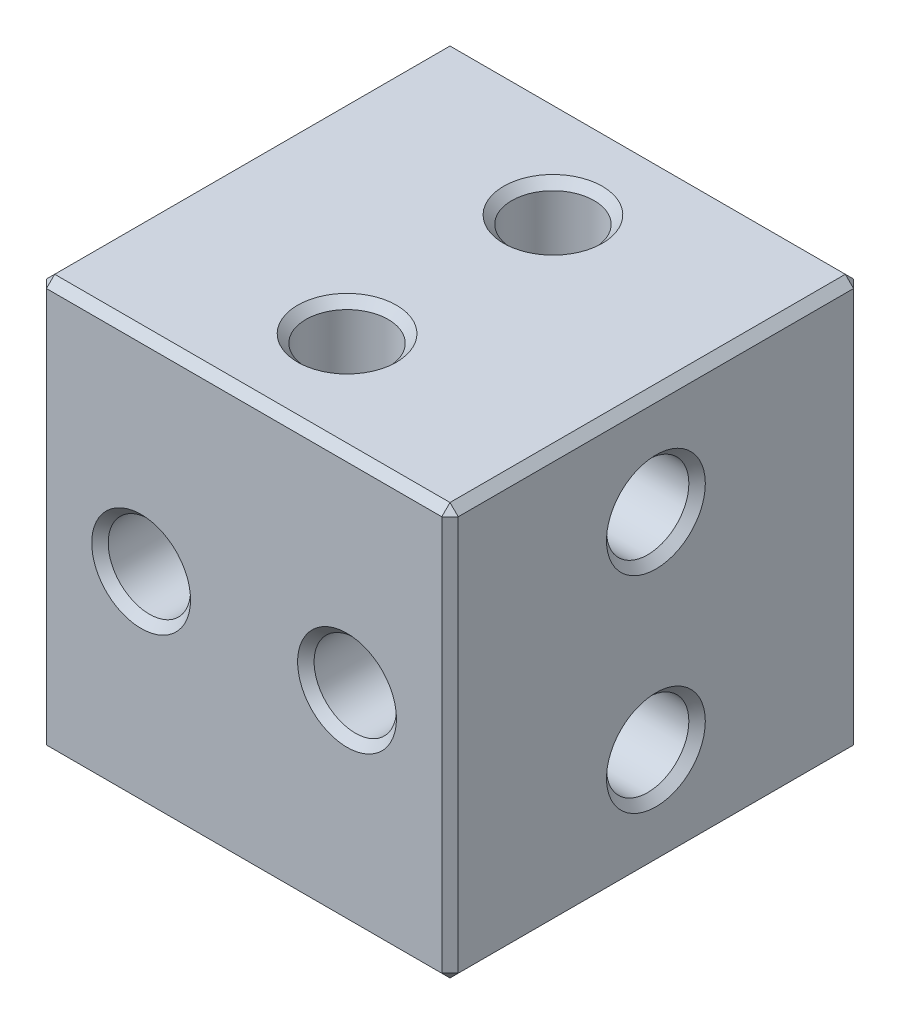
SolidWorks part; units mm, degrees
ref_plane "Front Plane" through (0, 0, 0) normal (0, 0, 1) x (1, 0, 0)
ref_plane "Top Plane" through (0, 0, 0) normal (0, 1, 0) x (1, 0, 0)
ref_plane "Right Plane" through (0, 0, 0) normal (1, 0, 0) x (0, 0, -1)
sketch "Sketch1" plane through (0, 0, 0) normal (0, 0, 1) x (1, 0, 0)
  line L0 (0, 38.089) -> (0, -37.1739) construction
  line L1 (-5, 5) -> (5, -5) construction
  line L2 (-5, 5) -> (5, 5)
  line L3 (-5, 5) -> (-5, -5)
  line L4 (-5, -5) -> (5, -5)
  line L5 (5, 5) -> (5, -5)
  line L6 (5, 5) -> (-5, -5) construction
  dimension "D1" = 10
  dimension "D2" = 10
extrude "Boss-Extrude1" add sketch "Sketch1" along normal blind 10
sketch "Sketch2" plane through (0, 0, 10) normal (0, 0, 1) x (1, 0, 0)
  line L0 (0, 6.9914) -> (0, -10.1171) construction
  circle A0 centre (-2.5, 0) radius 1
  circle A1 centre (2.5, 0) radius 1
  dimension "D1" = 2
  dimension "D2" = 5
extrude "Cut-Extrude1" cut sketch "Sketch2" against normal through all
sketch "Sketch3" plane through (0, 5, 0) normal (0, 1, 0) x (1, 0, 0)
  line L0 (5.3801, -5) -> (-5.5778, -5) construction
  line L1 (5, 0) -> (-5, -10) construction
  line L2 (5, -10) -> (-5, 0) construction
  circle A0 centre (0, -7.5) radius 1
  circle A1 centre (0, -2.5) radius 1
  point P2 (0, -5)
  dimension "D3" = 2
  dimension "D1" = 5
extrude "Cut-Extrude2" cut sketch "Sketch3" against normal through all
sketch "Sketch5" plane through (5, 0, 0) normal (1, 0, 0) x (0, 0, -1)
  line L0 (2.556, 0) -> (-10.2927, 0) construction
  line L2 (0, -5) -> (-10, 5) construction
  line L3 (-10, -5) -> (0, 5) construction
  circle A0 centre (-5, 2.5) radius 1
  circle A1 centre (-5, -2.5) radius 1
  point P15 (-5, 0)
  dimension "D3" = 2
  dimension "D2" = 5
extrude "Cut-Extrude4" cut sketch "Sketch5" against normal through all
chamfer "Chamfer1" distance 0.2 distance2 0.2 12 edges at (0, -5, 10) (-5, -5, 5) (-5, 0, 10) (5, 0, 10) (5, -5, 5) (0, -5, 0) (5, 0, 0) (-5, 0, 0) (-5, 5, 5) (0, 5, 10) (5, 5, 5) (0, 5, 0)
chamfer "Chamfer2" distance 0.2 distance2 0.2 12 edges at (-1.5, 0, 0) (1.5, 0, 0) (-1.5, 0, 10) (1.5, 0, 10) (0, 5, 3.5) (0, 5, 6.5) (-5, -3.5, 5) (-5, 3.5, 5) (0, -5, 3.5) (0, -5, 6.5) (5, 3.5, 5) (5, -3.5, 5)
